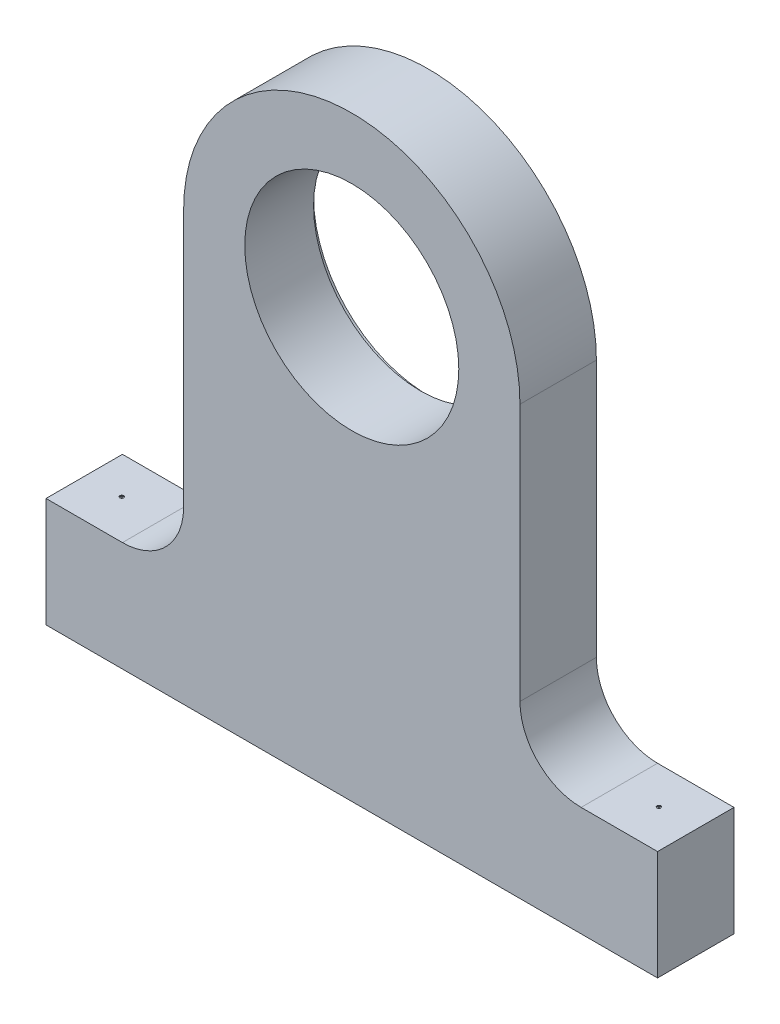
SolidWorks part; units mm, degrees
ref_plane "Front Plane" through (0, 0, 0) normal (0, 0, 1) x (1, 0, 0)
ref_plane "Top Plane" through (0, 0, 0) normal (0, 1, 0) x (1, 0, 0)
ref_plane "Right Plane" through (0, 0, 0) normal (1, 0, 0) x (0, 0, -1)
sketch "Sketch1" plane through (0, 0, 0) normal (0, 0, 1) x (1, 0, 0)
  line L0 (-228.5448, -223.1343) -> (271.4552, -223.1343)
  line L1 (271.4552, -223.1343) -> (271.4552, -133.5821)
  line L2 (271.4552, -133.5821) -> (158.9552, -133.5821)
  line L3 (158.9552, -133.5821) -> (158.9552, 126.8657)
  line L4 (-228.5448, -223.1343) -> (-228.5448, -133.5821)
  line L5 (-228.5448, -133.5821) -> (-116.0448, -133.5821)
  line L6 (-116.0448, -133.5821) -> (-116.0448, 126.8657)
  arc A0 (-116.0448, 126.8657) -> (158.9552, 126.8657) centre (21.4552, 126.8657) cw
  circle A1 centre (21.4552, 126.8657) radius 87.5
  point P10 (271.4552, -178.3582)
  dimension "D1" = 500
  dimension "D3" = 175
  dimension "D4" = 50
  dimension "D5" = 350
  dimension "D6" = 112.5
extrude "Boss-Extrude1" add sketch "Sketch1" along normal blind 62.5
fillet "Fillet1" radius 50 2 edges at (-116.0448, -133.5821, 31.25) (158.9552, -133.5821, 31.25)
sketch "Sketch2" plane through (0, 0, 0) normal (0, 0, 1) x (1, 0, 0)
  circle A0 centre (21.4552, 126.8657) radius 93.75
  dimension "D1" = 187.5
extrude "Cut-Extrude3" cut sketch "Sketch2" along normal blind 6.25
hole_wizard "CBORE for #00 Binding Head Machine Screw1" positions "Sketch3" profile "Sketch4" counterbore size "#00" standard "ANSI Inch" end condition through all
sketch "Sketch3" plane through (0, -133.5821, 0) normal (0, 1, 0) x (1, 0, 0)
  point P0 (-198.7985, -30.3253)
  point P2 (240.4122, -30.3253)
sketch "Sketch4" plane through (-198.7985, -133.5821, 30.3253) normal (1, 0, 0) x (0, 0, 1)
  line L0 (0, 0) -> (0, 89.5522)
  line L1 (0, 89.5522) -> (0.6985, 89.5522)
  line L3 (0.6985, 89.5522) -> (0.6985, 0.7112)
  line L4 (0.6985, 0.7112) -> (1.5875, 0.7112)
  line L5 (1.5875, 0.7112) -> (1.5875, 0)
  line L7 (1.5875, 0) -> (0, 0)
  line L11 (0, -6.35) -> (0, 107.95) construction
  dimension "Thru Hole Dia." = 1.397
  dimension "Thru Hole Depth" = 89.5522
  dimension "C'Bore Dia." = 3.175
  dimension "C'Bore Depth" = 0.7112
